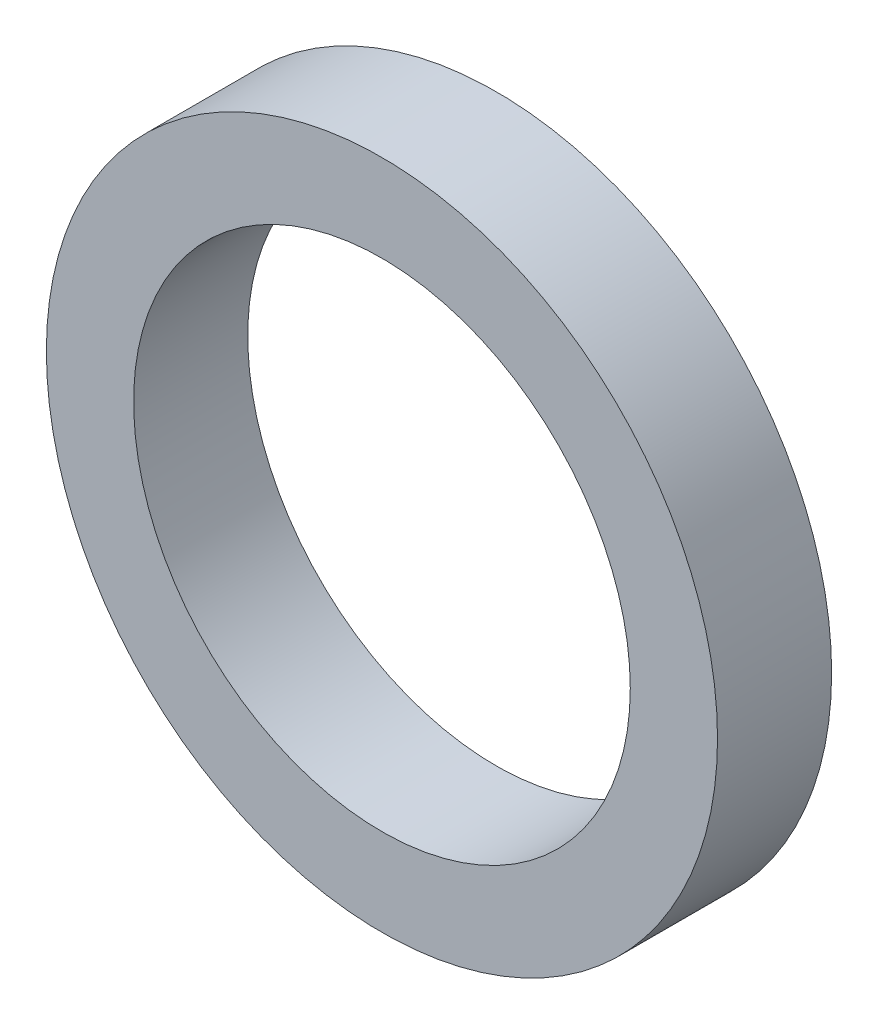
SolidWorks part; units mm, degrees
ref_plane "Front Plane" through (0, 0, 0) normal (0, 0, 1) x (1, 0, 0)
ref_plane "Top Plane" through (0, 0, 0) normal (0, 1, 0) x (1, 0, 0)
ref_plane "Right Plane" through (0, 0, 0) normal (1, 0, 0) x (0, 0, -1)
sketch "Sketch1" plane through (0, 0, 0) normal (0, 0, 1) x (1, 0, 0)
  circle A0 centre (0, 0) radius 7.5
  circle A1 centre (0, 0) radius 5.55
  dimension "D1" = 1.95
  dimension "D2" = 15
extrude "Boss-Extrude1" add sketch "Sketch1" along normal blind 2.55
